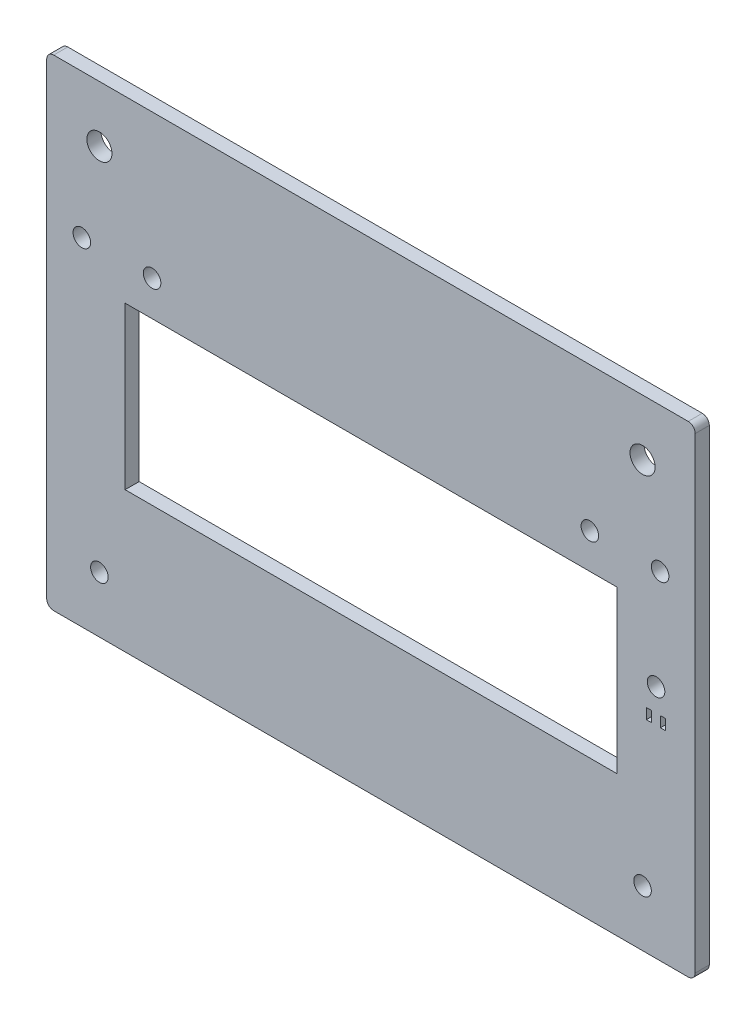
SolidWorks part; units mm, degrees
ref_plane "Front" through (0, 0, 0) normal (0, 0, 1) x (1, 0, 0)
ref_plane "Top" through (0, 0, 0) normal (0, 1, 0) x (1, 0, 0)
ref_plane "Right" through (0, 0, 0) normal (1, 0, 0) x (0, 0, -1)
sketch "Sketch1" plane through (0, 0, 0) normal (0, 0, 1) x (1, 0, 0)
  line L1 (0, 137) -> (184.64, 137)
  line L2 (0, 137) -> (0, 0)
  line L3 (0, 0) -> (184.64, 0)
  line L4 (184.64, 137) -> (184.64, 0)
  line L5 (40, 106) -> (40, 86)
  line L6 (40, 86) -> (22.32, 86)
  line L7 (22.32, 86) -> (22.32, 56)
  line L8 (22.32, 56) -> (162.32, 56)
  line L9 (162.32, 56) -> (162.32, 86)
  line L10 (162.32, 86) -> (144.64, 86)
  line L11 (144.64, 86) -> (144.64, 106)
  line L14 (144.64, 106) -> (40, 106)
  line L17 (92.32, 106) -> (92.32, 56) construction
  circle A0 centre (15, 16) radius 3.65
  circle A3 centre (169.64, 16) radius 3.65
  circle A5 centre (15, 121) radius 3.57
  circle A6 centre (30, 96) radius 2.5
  circle A8 centre (169.64, 121) radius 3.57
  circle A9 centre (154.64, 96) radius 2.5
  point P47 (40, 96)
  point P48 (144.64, 96)
  point P54 (92.32, 137)
  dimension "D4" = 5
  dimension "D5" = 5
  dimension "D13" = 7.3
  dimension "D14" = 7.3
  dimension "D17" = 7.14
  dimension "D18" = 7.14
  dimension "D11" = 20
  dimension "D19" = 10
  dimension "D20" = 10
  dimension "D24" = 30
  dimension "D30" = 16
  dimension "D31" = 16
  dimension "D9" = 140
  dimension "D10" = 104.64
  dimension "D12" = 40
  dimension "D7" = 25
  dimension "D6" = 15
  dimension "D8" = 15
  dimension "D15" = 30
extrude "Boss-Extrude1" add sketch "Sketch1" along normal blind 4
fillet "Fillet1" [suppressed] radius 2
sketch "Sketch2" [suppressed] plane through (0, 0, 4) normal (0, 0, 1) x (1, 0, 0)
  line L0 (20, 107) -> (20, 85)
  line L1 (20, 107) -> (37.32, 107)
  line L2 (20, 85) -> (22.32, 85)
  line L4 (164.64, 107) -> (164.64, 85)
  line L5 (40, 86) -> (22.32, 86) construction
  line L7 (164.64, 85) -> (162.32, 85)
  line L9 (144.64, 86) -> (144.64, 106) construction
  line L10 (40, 106) -> (40, 86) construction
  line L11 (22.32, 86) -> (22.32, 56) construction
  line L12 (162.32, 56) -> (162.32, 86) construction
  line L13 (37.32, 107) -> (37.32, 121)
  line L14 (37.32, 121) -> (147.32, 121)
  line L15 (147.32, 121) -> (147.32, 107)
  line L16 (147.32, 107) -> (164.64, 107)
  line L17 (22.32, 56) -> (162.32, 56) construction
  point P4 (92.32, 56)
  point P21 (92.32, 121)
  dimension "D3" = 20
  dimension "D2" = 1
  dimension "D4" = 20
  dimension "D1" = 14
  dimension "D5" = 110
  dimension "D6" = 22
extrude "Cut-Extrude1" [suppressed] cut sketch "Sketch2" against normal through all
sketch "Sketch3" plane through (0, 0, 4) normal (0, 0, 1) x (1, 0, 0)
  line L1 (40, 86) -> (144.64, 86)
  line L2 (40, 86) -> (40, 106)
  line L3 (40, 106) -> (144.64, 106)
  line L4 (144.64, 86) -> (144.64, 106)
extrude "Boss-Extrude2" add sketch "Sketch3" against normal blind 4
sketch "Sketch5" [suppressed] plane through (0, 0, 4) normal (0, 0, 1) x (1, 0, 0)
  line L0 (79.32, 48) -> (105.32, 48) construction
  line L1 (79.32, 48) -> (79.32, 22) construction
  line L3 (22.32, 56) -> (162.32, 56) construction
  line L5 (0, 0) -> (184.64, 0) construction
  circle A0 centre (92.32, 35) radius 11
  circle A1 centre (79.32, 48) radius 1.5
  circle A2 centre (105.32, 48) radius 1.5
  circle A3 centre (79.32, 22) radius 1.5
  circle A4 centre (105.32, 22) radius 1.5
  point P10 (92.32, 48)
  point P11 (79.32, 35)
  point P14 (92.32, 0)
  dimension "D3" = 22
  dimension "D5" = 3
  dimension "D6" = 3
  dimension "D7" = 3
  dimension "D8" = 3
  dimension "D1" = 26
  dimension "D2" = 26
  dimension "D4" = 8
extrude "Cut-Extrude3" [suppressed] cut sketch "Sketch5" against normal through all
sketch "Sketch6" plane through (0, 0, 4) normal (0, 0, 1) x (1, 0, 0)
  line L0 (67.32, 16) -> (117.32, 16) construction
  line L1 (0, 0) -> (184.64, 0) construction
  circle A0 centre (67.32, 16) radius 3.65
  circle A1 centre (117.32, 16) radius 3.65
  point P4 (92.32, 16)
  point P9 (92.32, 0)
  dimension "D2" = 7.3
  dimension "D3" = 7.3
  dimension "D1" = 50
extrude "Cut-Extrude4" cut sketch "Sketch6" against normal through all
sketch "Sketch7" [suppressed] plane through (0, 0, 4) normal (0, 0, 1) x (1, 0, 0)
  line L0 (0, 137) -> (0, 0) construction
  line L1 (184.64, 0) -> (184.64, 137) construction
  line L2 (22.32, 56) -> (162.32, 56) construction
  circle A0 centre (7, 51.5) radius 0.8
  circle A1 centre (7, 40.5) radius 0.8
  circle A2 centre (177.64, 51.5) radius 0.8
  circle A3 centre (177.64, 40.5) radius 0.8
  dimension "D4" = 1.6
  dimension "D5" = 1.6
  dimension "D6" = 1.6
  dimension "D7" = 1.6
  dimension "D1" = 7
  dimension "D2" = 11
  dimension "D3" = 7
  dimension "D8" = 4.5
extrude "Cut-Extrude5" [suppressed] cut sketch "Sketch7" against normal blind 10
sketch "Sketch8" plane through (0, 0, 4) normal (0, 0, 1) x (1, 0, 0)
  line L1 (22.32, 56) -> (162.32, 56)
  line L2 (22.32, 56) -> (22.32, 40)
  line L3 (22.32, 40) -> (162.32, 40)
  line L4 (162.32, 56) -> (162.32, 40)
  dimension "D1" = 16
extrude "Cut-Extrude6" cut sketch "Sketch8" against normal blind 10
fillet "Fillet2" [suppressed] radius 40
sketch "Sketch9" plane through (0, 0, 4) normal (0, 0, 1) x (1, 0, 0)
  line L0 (184.64, 137) -> (0, 137) construction
  line L1 (0, 137) -> (20, 137)
  line L2 (0, 137) -> (0, 130)
  line L3 (0, 130) -> (20, 130)
  line L4 (20, 137) -> (20, 130)
  line L5 (184.64, 137) -> (164.64, 137)
  line L6 (184.64, 137) -> (184.64, 130)
  line L7 (184.64, 130) -> (164.64, 130)
  line L8 (164.64, 137) -> (164.64, 130)
  line L9 (184.64, 0) -> (164.64, 0)
  line L10 (184.64, 0) -> (184.64, 7)
  line L11 (184.64, 7) -> (164.64, 7)
  line L12 (164.64, 0) -> (164.64, 7)
  line L13 (0, 0) -> (20, 0)
  line L14 (0, 0) -> (0, 7)
  line L15 (0, 7) -> (20, 7)
  line L16 (20, 0) -> (20, 7)
  line L17 (0, 137) -> (0, 0) construction
  line L18 (184.64, 0) -> (184.64, 137) construction
  line L19 (0, 0) -> (184.64, 0) construction
  dimension "D3" = 20
  dimension "D1" = 7
  dimension "D2" = 20
  dimension "D4" = 7
extrude "Cut-Extrude7" [suppressed] cut sketch "Sketch9" against normal through all
fillet "Fillet3" [suppressed] radius 2
fillet "Fillet4" [suppressed] radius 2
fillet "Fillet5" radius 2 4 edges at (0, 0, 2) (0, 137, 2) (184.64, 137, 2) (184.64, 0, 2)
sketch "Sketch10" plane through (0, 0, 4) normal (0, 0, 1) x (1, 0, 0)
  line L0 (184.64, 2) -> (184.64, 135) construction
  line L1 (0, 23.2942) -> (184.64, 23.2942)
  line L2 (0, 23.2942) -> (0, 8.7058)
  line L3 (0, 8.7058) -> (184.64, 8.7058)
  line L4 (184.64, 23.2942) -> (184.64, 8.7058)
  line L5 (0, 135) -> (0, 2) construction
  circle A0 centre (15, 16) radius 2.5
  circle A1 centre (169.64, 16) radius 2.5
  circle A2 centre (117.32, 16) radius 2.5
  circle A3 centre (67.32, 16) radius 2.5
  point P16 (0, 16)
  circle M2 centre (117.32, 16) radius 3.65
  circle M3 centre (67.32, 16) radius 3.65
  circle M11 centre (15, 16) radius 3.65
  circle M20 centre (169.64, 16) radius 3.65
  dimension "D4" = 5
  dimension "D1" = 5
  dimension "D2" = 5
  dimension "D3" = 5
extrude "Boss-Extrude3" [suppressed] add sketch "Sketch10" against normal through all contours A0 M11 | A3 M3 | A2 M2 | A1 M20
sketch "Sketch11" plane through (0, 0, 4) normal (0, 0, 1) x (1, 0, 0)
  line L0 (67.32, 16) -> (117.32, 16) construction
  line L1 (0, 23.5) -> (184.64, 23.5)
  line L2 (0, 23.5) -> (0, 8.5)
  line L3 (0, 8.5) -> (184.64, 8.5)
  line L4 (184.64, 23.5) -> (184.64, 8.5)
  line L5 (0, 135) -> (0, 2) construction
  circle A0 centre (15, 16) radius 2.5
  circle A1 centre (169.64, 16) radius 2.5
  point P12 (92.32, 23.5)
  point P13 (184.64, 16)
  point P15 (92.32, 16)
  dimension "D4" = 5
  dimension "D3" = 5
  dimension "D1" = 15
extrude "Boss-Extrude4" add sketch "Sketch11" against normal through all contours L3 L4 L1 L2
sketch "Sketch12" plane through (0, 0, 4) normal (0, 0, 1) x (1, 0, 0)
  circle A0 centre (10, 96) radius 2.5
  circle A1 centre (174.64, 96) radius 2.5
  dimension "D3" = 20
  dimension "D4" = 20
  dimension "D1" = 5
  dimension "D2" = 5
extrude "Cut-Extrude8" cut sketch "Sketch12" against normal through all
sketch "Sketch13" plane through (0, 0, 4) normal (0, 0, 1) x (1, 0, 0)
  line L0 (184.64, 63) -> (162.32, 63) construction
  line L3 (162.32, 40) -> (162.32, 86) construction
  line L4 (184.64, 2) -> (184.64, 135) construction
  circle A0 centre (173.48, 67) radius 2.5
  point P6 (162.32, 63)
  point P8 (173.48, 63)
  dimension "D1" = 5
  dimension "D2" = 4
extrude "Cut-Extrude9" cut sketch "Sketch13" against normal blind 10
sketch "Sketch14" plane through (0, 0, 4) normal (0, 0, 1) x (1, 0, 0)
  line L0 (172.23, 60.5) -> (174.73, 60.5) construction
  line L1 (170.73, 60.5) -> (172.23, 60.5)
  line L2 (170.73, 60.5) -> (170.73, 57.5)
  line L3 (170.73, 57.5) -> (172.23, 57.5)
  line L4 (172.23, 60.5) -> (172.23, 57.5)
  line L5 (174.73, 60.5) -> (176.23, 60.5)
  line L6 (174.73, 60.5) -> (174.73, 57.5)
  line L7 (174.73, 57.5) -> (176.23, 57.5)
  line L8 (176.23, 60.5) -> (176.23, 57.5)
  circle A1 centre (173.48, 67) radius 2.5 construction
  point P8 (173.48, 67)
  point P9 (173.48, 60.5)
  point P13 (173.48, 64.5)
  dimension "D1" = 1.5
  dimension "D2" = 1.5
  dimension "D3" = 2.5
  dimension "D4" = 3
  dimension "D5" = 4
extrude "Cut-Extrude10" cut sketch "Sketch14" against normal through all
equation "\"D13@Sketch1\"=\"D14@Sketch1\""
equation "\"D17@Sketch1\"=\"D18@Sketch1\""
equation "\"D19@Sketch1\"=\"D20@Sketch1\""
equation "\"D3@Sketch6\"=\"D2@Sketch6\""
equation "\"D30@Sketch1\"=\"D31@Sketch1\""
equation "\"D3@Sketch2\"=\"D4@Sketch2\""
equation "\"D3@Sketch7\"=\"D1@Sketch7\""
equation "\"D5@Sketch7\"=\"D4@Sketch7\""
equation "\"D6@Sketch7\"=\"D4@Sketch7\""
equation "\"D7@Sketch7\"=\"D4@Sketch7\""
equation "\"D3@Sketch9\"=\"D2@Sketch9\""
equation "\"D4@Sketch9\"=\"D1@Sketch9\""
equation "\"D2@Sketch10\"=\"D1@Sketch10\""
equation "\"D3@Sketch10\"=\"D1@Sketch10\""
equation "\"D4@Sketch10\"=\"D1@Sketch10\""
equation "\"D3@Sketch11\"=\"D4@Sketch11\""
equation "\"D2@Sketch12\"=\"D1@Sketch12\""
equation "\"D6@Sketch5\"=\"D5@Sketch5\""
equation "\"D7@Sketch5\"=\"D5@Sketch5\""
equation "\"D8@Sketch5\"=\"D5@Sketch5\""
equation "\"D8@Sketch1\"=\"D6@Sketch1\""
equation "\"D4@Sketch12\"=\"D3@Sketch12\""
equation "\"D2@Sketch14\"=\"D1@Sketch14\""
